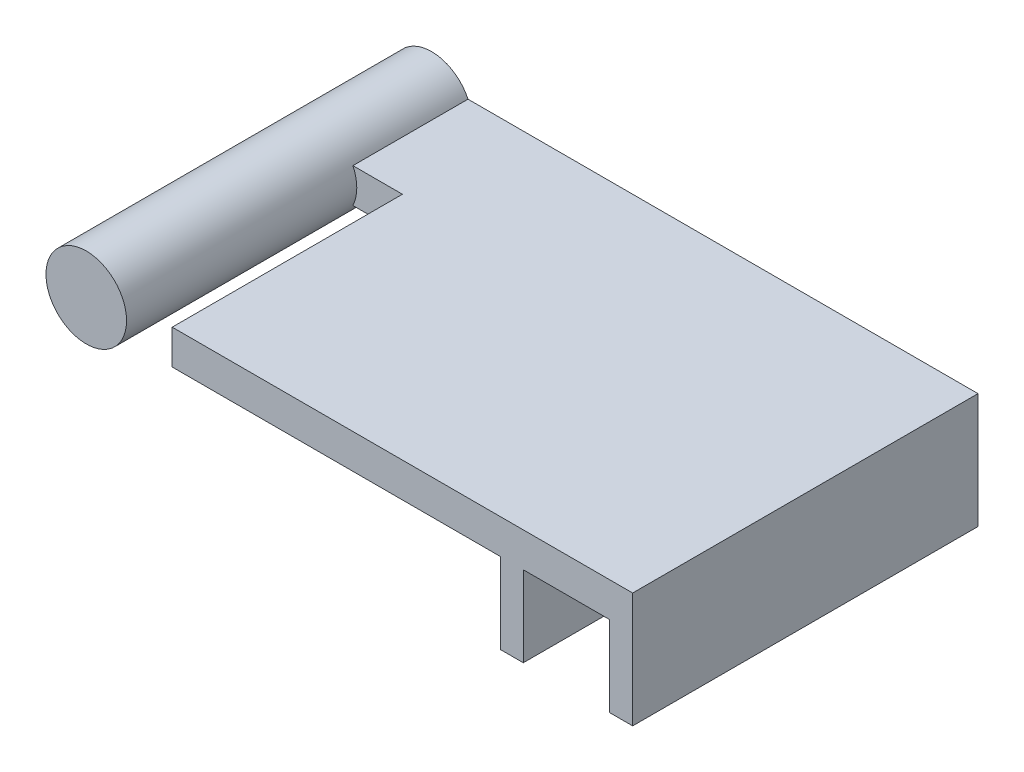
SolidWorks part; units mm, degrees
ref_plane "Front Plane" through (0, 0, 0) normal (0, 0, 1) x (1, 0, 0)
ref_plane "Top Plane" through (0, 0, 0) normal (0, 1, 0) x (1, 0, 0)
ref_plane "Right Plane" through (0, 0, 0) normal (1, 0, 0) x (0, 0, -1)
sketch "Sketch2" plane through (0, 0, 0) normal (0, 0, 1) x (1, 0, 0)
  line L0 (18, -8.5) -> (10.5, -8.5) construction
  line L1 (-20, -1.5) -> (8.5, -1.5)
  line L2 (-20, -1.5) -> (-20, 1.5)
  line L3 (-20, 1.5) -> (20, 1.5)
  line L4 (20, -1.5) -> (20, 1.5)
  line L5 (-20, -1.5) -> (20, 1.5) construction
  line L6 (-20, 1.5) -> (20, -1.5) construction
  line L8 (20, -1.5) -> (20, -8.5)
  line L9 (20, -8.5) -> (18, -8.5)
  line L10 (18, -1.5) -> (18, -8.5)
  line L15 (10.5, -1.5) -> (18, -1.5)
  line L16 (10.5, -8.5) -> (8.5, -8.5)
  line L17 (10.5, -8.5) -> (10.5, -1.5)
  line L19 (8.5, -8.5) -> (8.5, -1.5)
  point P0 (0, 0)
  dimension "D1" = 40
  dimension "D2" = 3
  dimension "D3" = 7.5
  dimension "D4" = 2
  dimension "D5" = 7
  dimension "D6" = 2
extrude "Boss-Extrude1" add sketch "Sketch2" along normal blind 30
sketch "Sketch3" plane through (0, 0, 0) normal (0, 0, 1) x (1, 0, 0)
  line L0 (-20, 1.5) -> (-20, -1.5) construction
  line L1 (-20, -1.5) -> (-26, -1.5)
  line L2 (-20, -1.5) -> (-20, 1.5)
  line L3 (-20, 1.5) -> (-26, 1.5)
  line L4 (-26, -1.5) -> (-26, 1.5)
  line L5 (-20, -1.5) -> (8.5, -1.5) construction
  dimension "D1" = 6
extrude "Boss-Extrude2" add sketch "Sketch3" along normal blind 10
sketch "Sketch4" plane through (0, 0, 0) normal (0, 0, 1) x (1, 0, 0)
  circle A0 centre (-27.4651, 0) radius 3.5
  dimension "D1" = 7
extrude "Boss-Extrude3" add sketch "Sketch4" along normal blind 30
